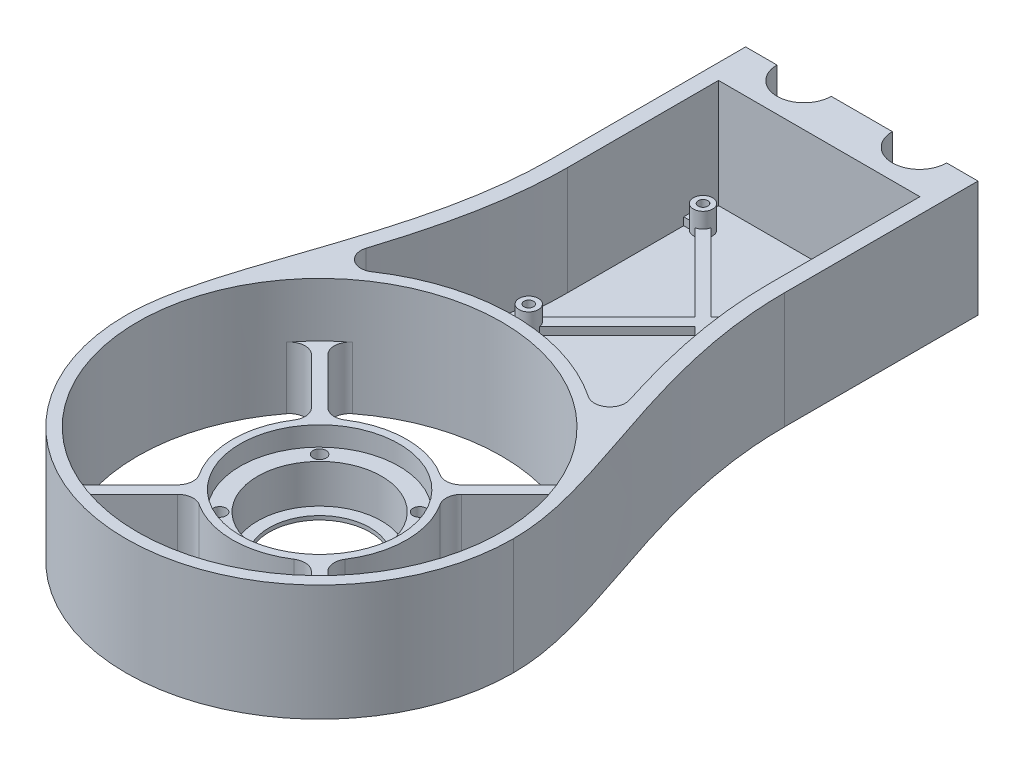
SolidWorks part; units mm, degrees
material "3.1355 (EN-AW 2024)"
ref_plane "Front" through (0, 0, 0) normal (0, 0, 1) x (1, 0, 0)
ref_plane "Top" through (0, 0, 0) normal (0, 1, 0) x (1, 0, 0)
ref_plane "Right" through (0, 0, 0) normal (1, 0, 0) x (0, 0, -1)
sketch "Эскиз1" plane through (0, 0, 0) normal (0, 1, 0) x (1, 0, 0)
  line L0 (0, 0) -> (8.1, 0)
  line L1 (0, 0) -> (0, -100) construction
  line L2 (0, -12.5175) -> (60, -12.5175) construction
  line L3 (8.1, 0) -> (22.1, 0) construction
  line L4 (30, -12.5175) -> (30, 0) construction
  line L5 (60, 0) -> (51.9, 0)
  line L6 (60, 0) -> (60, -100) construction
  line L7 (22.1, 0) -> (37.9, 0)
  line L8 (30, 0) -> (30, -140) construction
  line L9 (0, -80.7644) -> (0, -19.2352) construction
  line L10 (0, 0) -> (0, -50)
  line L11 (60, 0) -> (60, -50)
  arc A0 (22.1, 0) -> (8.1, 0) centre (15.1, 0) cw
  arc A1 (37.9, 0) -> (51.9, 0) centre (44.9, 0) ccw
  circle A2 centre (30, -140) radius 47 construction
  circle A3 centre (30, -140) radius 50 construction
  arc A4 (-20, -140) -> (80, -140) centre (30, -140) ccw
  spline S0 degree 3 poles (0, -50) (0, -86.1164) (-20.1607, -116.6426) (-20, -140) knots 0 0 0 0 1 1 1 1
  spline S1 degree 3 poles (60, -50) (60, -86.1164) (80.1607, -116.6426) (80, -140) knots 0 0 0 0 1 1 1 1
  dimension "D3" = 7
  dimension "D5" = 94
  dimension "D6" = 100
  dimension "D1" = 60
  dimension "D2" = 29.8
  dimension "D4" = 140
extrude "Бобышка-Вытянуть1" add sketch "Эскиз1" along normal blind 30
sketch "Эскиз2" plane through (0, 0, 0) normal (0, -1, 0) x (1, 0, 0)
  line L10 (3, 50) -> (3, 3)
  line L11 (3, 3) -> (5.5606, 3)
  line L12 (24.6394, 3) -> (35.3606, 3)
  line L13 (54.4394, 3) -> (57, 3)
  line L14 (57, 3) -> (57, 50)
  line L15 (0, 50) -> (0, 0)
  line L16 (60, 0) -> (60, 50)
  line L17 (51.9, 0) -> (60, 0)
  line L18 (22.1, 0) -> (37.9, 0)
  line L19 (0, 0) -> (8.1, 0)
  line L20 (0, 50) -> (0, 0) construction
  line L21 (60, 0) -> (60, 50) construction
  line L22 (51.9, 0) -> (60, 0) construction
  line L23 (22.1, 0) -> (37.9, 0) construction
  line L24 (0, 0) -> (8.1, 0) construction
  arc A6 (24.6394, 3) -> (5.5606, 3) centre (15.1, 0) ccw
  arc A7 (54.4394, 3) -> (35.3606, 3) centre (44.9, 0) ccw
  arc A8 (77, 139.9896) -> (-17, 139.9896) centre (30, 140) ccw
  arc A9 (80, 140) -> (-20, 140) centre (30, 140) ccw
  arc A10 (51.9, 0) -> (37.9, 0) centre (44.9, 0) ccw
  arc A11 (22.1, 0) -> (8.1, 0) centre (15.1, 0) ccw
  arc A12 (80, 140) -> (-20, 140) centre (30, 140) ccw construction
  arc A13 (51.9, 0) -> (37.9, 0) centre (44.9, 0) ccw construction
  arc A14 (22.1, 0) -> (8.1, 0) centre (15.1, 0) ccw construction
  spline S4 degree 1 poles (57, 50) (77, 139.9896) knots 0 0 1 1 construction
  spline S5 degree 1 poles (-17, 139.9896) (3, 50) knots 0 0 1 1 construction
  spline S6 degree 3 poles (1977.4891, 89.0603) (-2125.3468, 381.0882) (2082.0698, -1.9555) (-1932.4354, -415.3328) knots -3.22742 -3.22742 -3.22742 -3.22742 4.19175 4.19175 4.19175 4.19175 only from (-20, 140) to (0, 50)
  spline S7 degree 3 poles (1992.5098, -415.3405) (-2022.1214, -1.9603) (2185.3713, 381.0899) (-1917.4879, 89.0604) knots -3.191796 -3.191796 -3.191796 -3.191796 4.227419 4.227419 4.227419 4.227419 only from (60, 50) to (80, 140)
  spline S8 degree 3 poles (-20, 140) (-20.1607, 116.6426) (0, 86.1164) (0, 50) knots 0 0 0 0 1 1 1 1 construction
  spline S9 degree 3 poles (60, 50) (60, 86.1164) (80.1607, 116.6426) (80, 140) knots 0 0 0 0 1 1 1 1 construction
  spline S10 degree 3 poles (57, 50) (57, 51.1576) (57.0406, 53.4814) (57.2737, 58.0563) (57.8301, 63.6858) (58.8583, 70.2789) (60.6259, 78.8547) (63.4225, 89.1628) (67.2235, 100.8568) (70.9828, 111.8512) (73.6804, 120.3995) (75.3444, 126.839) (76.2902, 131.4603) (76.7834, 135.1232) (76.9778, 137.9484) (77.0049, 139.3044) (77, 139.9896) knots 0 0 0 0 0.031255 0.06251 0.12502 0.18753 0.25004 0.375059 0.500079 0.625099 0.750119 0.812629 0.875139 0.937649 0.968904 1.000159 1.000159 1.000159 1.000159
  spline S11 degree 3 poles (-17, 139.9896) (-17.0049, 139.3044) (-16.9778, 137.9484) (-16.7834, 135.1232) (-16.2902, 131.4603) (-15.3444, 126.839) (-13.6804, 120.3995) (-10.9828, 111.8512) (-7.2235, 100.8568) (-3.4225, 89.1628) (-0.6259, 78.8547) (1.1417, 70.2789) (2.1699, 63.6858) (2.7263, 58.0563) (2.9594, 53.4814) (3, 51.1576) (3, 50) knots -0.000159 -0.000159 -0.000159 -0.000159 0.031096 0.062351 0.124861 0.187371 0.249881 0.374901 0.499921 0.624941 0.74996 0.81247 0.87498 0.93749 0.968745 1 1 1 1
  dimension "D1" = 0
  dimension "D2" = 3
extrude "Вырез-Вытянуть1" cut sketch "Эскиз2" against normal through all
sketch "Эскиз3" plane through (0, 0, 0) normal (0, -1, 0) x (1, 0, 0)
  circle A0 centre (30, 140) radius 13
  circle A1 centre (30, 140) radius 22.5
  dimension "D1" = 26
  dimension "D2" = 45
extrude "Бобышка-Вытянуть2" add sketch "Эскиз3" against normal blind 16 separate body
sketch "Эскиз4" plane through (0, 16, 0) normal (0, 1, 0) x (1, 0, 0)
  circle A2 centre (30, -140) radius 20.5
  dimension "D1" = 41
extrude "Вырез-Вытянуть2" cut sketch "Эскиз4" against normal blind 5
sketch "Эскиз5" plane through (0, 11, 0) normal (0, 1, 0) x (1, 0, 0)
  circle A0 centre (30, -140) radius 16
  dimension "D1" = 32
extrude "Вырез-Вытянуть3" cut sketch "Эскиз5" against normal blind 10
sketch "Эскиз6" plane through (0, 11, 0) normal (0, 1, 0) x (1, 0, 0)
  line L0 (30, -140) -> (11.75, -140) construction
  line L1 (30, -140) -> (17.0953, -127.0953) construction
  line L2 (30, -140) -> (42.9047, -127.0953) construction
  line L3 (30, -140) -> (42.9047, -152.9047) construction
  line L4 (30, -140) -> (17.0953, -152.9047) construction
  circle A0 centre (30, -140) radius 18.25 construction
  point P11 (30, -140)
  dimension "D1" = 36.5
  dimension "D2" = 45
  dimension "D3" = 4
hole_wizard "Отверстие с зазором M31" positions "Эскиз8" profile "Эскиз7" hole size "M3" standard "Ansi Metric" end condition through all
sketch "Эскиз8" plane through (0, 11, 0) normal (0, 1, 0) x (1, 0, 0)
  point P0 (17.0953, -127.0953)
  point P3 (42.9047, -127.0953)
  point P6 (42.9047, -152.9047)
  point P9 (17.0953, -152.9047)
sketch "Эскиз7" plane through (17.0953, 11, 127.0953) normal (1, 0, 0) x (0, 0, 1)
  line L0 (0, 0) -> (0, 11)
  line L1 (0, 11) -> (1.7, 11)
  line L2 (1.7, 11) -> (1.7, 0)
  line L5 (1.7, 0) -> (0, 0)
  line L11 (0, -6.35) -> (0, 107.95) construction
  dimension "Диаметр сквозного отверстия" = 3.4
  dimension "Глубина сквозного отверстия" = 11
sketch "Эскиз9" plane through (0, 0, 0) normal (0, -1, 0) x (1, 0, 0)
  arc A0 (-10.5903, 110.8036) -> (70.5903, 110.8036) centre (30, 140) ccw
  arc A2 (-17, 139.9896) -> (77, 139.9896) centre (30, 140) ccw
  spline S1 degree 3 poles (176.8305, 2130.3757) (16.1333, 171.6325) (-19.1296, 169.2303) (-16.7834, 135.1232) (-16.2902, 131.4603) (-15.3444, 126.839) (-13.6804, 120.3995) (-10.9828, 111.8512) (-7.2235, 100.8568) (-3.4225, 89.1628) (-0.6259, 78.8547) (1.1417, 70.2789) (2.1699, 63.6858) (2.7263, 58.0563) (6.1081, -8.3152) (-50.2326, -100.9507) (-382.6813, 2011.3686) knots -1.384464 -1.384464 -1.384464 -1.384464 0.031096 0.062351 0.124861 0.187371 0.249881 0.374901 0.499921 0.624941 0.74996 0.81247 0.87498 0.93749 0.968745 2.688741 2.688741 2.688741 2.688741 only from (-17, 139.9896) to (3, 50) construction
  spline S2 degree 3 poles (442.6854, 2011.3946) (110.2331, -100.9514) (53.8919, -8.3154) (57.2737, 58.0563) (57.8301, 63.6858) (58.8583, 70.2789) (60.6259, 78.8547) (63.4225, 89.1628) (67.2235, 100.8568) (70.9828, 111.8512) (73.6804, 120.3995) (75.3444, 126.839) (76.2902, 131.4603) (76.7834, 135.1232) (79.1296, 169.2304) (43.8663, 171.6325) (-116.8331, 2130.4078) knots -1.688748 -1.688748 -1.688748 -1.688748 0.031255 0.06251 0.12502 0.18753 0.25004 0.375059 0.500079 0.625099 0.750119 0.812629 0.875139 0.937649 0.968904 2.384472 2.384472 2.384472 2.384472 only from (57, 50) to (77, 139.9896) construction
  spline S3 degree 3 poles (70.5903, 110.8036) (70.6927, 111.1128) (71.9682, 114.9738) (73.6804, 120.3995) (75.3444, 126.839) (76.2902, 131.4603) (76.7834, 135.1232) (76.9778, 137.9484) (77.0049, 139.3044) (77, 139.9896) knots 0.614251 0.614251 0.614251 0.614251 0.625099 0.750119 0.812629 0.875139 0.937649 0.968904 1.000159 1.000159 1.000159 1.000159
  spline S4 degree 3 poles (-17, 139.9896) (-17.0049, 139.3044) (-16.9778, 137.9484) (-16.7834, 135.1232) (-16.2902, 131.4603) (-15.3444, 126.839) (-13.6804, 120.3995) (-11.9682, 114.9738) (-10.6927, 111.1128) (-10.5903, 110.8036) knots -0.000159 -0.000159 -0.000159 -0.000159 0.031096 0.062351 0.124861 0.187371 0.249881 0.374901 0.385749 0.385749 0.385749 0.385749
extrude "Бобышка-Вытянуть3" add sketch "Эскиз9" against normal up to surface (16 mm away) up to face at (30, 16, 160.5)
sketch "Эскиз10" plane through (0, 0, 0) normal (0, -1, 0) x (1, 0, 0)
  line L0 (30, 140) -> (-3.2267, 106.7587) construction
  line L1 (30, 140) -> (-17, 139.9896) construction
  line L2 (13.0616, 154.8101) -> (-4.2848, 172.1489)
  line L3 (15.1899, 123.0616) -> (-2.1489, 105.7152)
  line L4 (13.068, 125.1825) -> (-4.2708, 107.8362)
  line L5 (31.0609, 138.9396) -> (-2.1658, 105.6982) construction
  line L6 (15.1825, 156.932) -> (-2.1638, 174.2708)
  line L7 (44.8101, 156.9384) -> (62.1489, 174.2848)
  line L8 (46.932, 154.8175) -> (64.2708, 172.1638)
  line L9 (46.9384, 125.1899) -> (64.2848, 107.8511)
  line L10 (44.8175, 123.068) -> (62.1638, 105.7292)
  circle A0 centre (30, 140) radius 22.5 construction
  arc A1 (13.068, 125.1825) -> (15.1899, 123.0616) centre (30, 140) ccw
  circle A2 centre (30, 140) radius 47 construction
  arc A3 (-4.2708, 107.8362) -> (-2.1489, 105.7152) centre (30, 140) ccw
  arc A4 (-2.1638, 174.2708) -> (-4.2848, 172.1489) centre (30, 140) ccw
  arc A5 (15.1825, 156.932) -> (13.0616, 154.8101) centre (30, 140) ccw
  arc A6 (64.2708, 172.1638) -> (62.1489, 174.2848) centre (30, 140) ccw
  arc A7 (46.932, 154.8175) -> (44.8101, 156.9384) centre (30, 140) ccw
  arc A8 (62.1638, 105.7292) -> (64.2848, 107.8511) centre (30, 140) ccw
  arc A9 (44.8175, 123.068) -> (46.9384, 125.1899) centre (30, 140) ccw
  point P5 (28.9391, 141.0604)
  point P9 (-4.2877, 107.8192)
  point P29 (30, 140)
  point P36 (30, 140)
  dimension "D1" = 45
  dimension "D2" = 4
  dimension "D3" = 1.5
extrude "Бобышка-Вытянуть4" add sketch "Эскиз10" against normal up to surface (16 mm away) up to face at (30, 16, 160.5)
fillet "Скругление1" radius 4 2 edges
fillet "Скругление2" radius 4 16 edges at (13.068, 8, 125.1825) (-4.2708, 8, 107.8362) (13.0616, 8, 154.8101) (-4.2848, 8, 172.1489) (-2.1638, 8, 174.2708) (15.1825, 8, 156.932) (44.8101, 8, 156.9384) (62.1489, 8, 174.2848) (46.932, 8, 154.8175) (64.2708, 8, 172.1638) (46.9384, 8, 125.1899) (64.2848, 8, 107.8511) (44.8175, 8, 123.068) (15.1899, 8, 123.0616) (-2.1489, 8, 105.7152) (62.1638, 8, 105.7292)
sketch "Эскиз11" plane through (0, 30, 0) normal (0, 1, 0) x (1, 0, 0)
  line L0 (3, -50) -> (3, -3) construction
  line L1 (3, -10) -> (57, -10)
  line L2 (57, -3) -> (57, -50) construction
  line L3 (54.4394, -3) -> (57, -3) construction
  line L4 (24.6394, -3) -> (35.3606, -3) construction
  line L5 (3, -3) -> (5.5606, -3) construction
  line L6 (54.4394, -3) -> (57, -3)
  line L7 (24.6394, -3) -> (35.3606, -3)
  line L8 (3, -3) -> (5.5606, -3)
  line L9 (3, -10) -> (3, -3)
  line L10 (57, -3) -> (57, -10)
  arc A0 (5.5606, -3) -> (24.6394, -3) centre (15.1, 0) ccw construction
  arc A1 (5.5606, -3) -> (24.6394, -3) centre (15.1, 0) ccw
  arc A2 (35.3606, -3) -> (54.4394, -3) centre (44.9, 0) ccw construction
  arc A3 (35.3606, -3) -> (54.4394, -3) centre (44.9, 0) ccw
  line M2 (3, -50) -> (3, -3)
  line M3 (3, -3) -> (5.5606, -3)
  arc M4 (5.5606, -3) -> (24.6394, -3) centre (15.1, 0) ccw
  line M5 (24.6394, -3) -> (35.3606, -3)
  arc M6 (35.3606, -3) -> (54.4394, -3) centre (44.9, 0) ccw
  line M7 (54.4394, -3) -> (57, -3)
  line M8 (57, -3) -> (57, -50)
extrude "Бобышка-Вытянуть5" add sketch "Эскиз11" against normal through all contours L1 M4 M6 M5 | L1 M6 M8 M7 | L1 M2 M4 M3
sketch "Эскиз12" plane through (0, 16, 0) normal (0, 1, 0) x (1, 0, 0)
  arc A0 (59.1694, -99.3903) -> (0.8306, -99.3903) centre (30, -140) ccw construction
  arc A1 (-5.3129, -94.9233) -> (0.8306, -99.3903) centre (-1.5029, -96.1415) ccw construction
  arc A2 (59.1694, -99.3903) -> (65.3129, -94.9233) centre (61.5029, -96.1415) ccw construction
  arc A3 (59.1694, -99.3903) -> (0.8306, -99.3903) centre (30, -140) ccw
  arc A4 (-5.3129, -94.9233) -> (0.8306, -99.3903) centre (-1.5029, -96.1415) ccw
  arc A5 (59.1694, -99.3903) -> (65.3129, -94.9233) centre (61.5029, -96.1415) ccw
  arc A7 (58.7182, -102.7943) -> (1.298, -102.7818) centre (30, -140) ccw construction
  arc A8 (77, -139.9896) -> (-17, -139.9896) centre (30, -140) ccw
  spline S0 degree 3 poles (-1914.7367, 431.9839) (72.5207, 220.6611) (28.2156, 2.7872) (-10.9828, -111.8512) (-13.6804, -120.3995) (-15.3444, -126.839) (-16.2902, -131.4603) (-16.7834, -135.1232) (-19.1296, -169.2301) (16.1331, -171.6324) (176.8285, -2130.3521) knots -3.597718 -3.597718 -3.597718 -3.597718 0.06297 0.187989 0.313009 0.375519 0.438029 0.500539 0.531794 1.947349 1.947349 1.947349 1.947349 only from (-5.3129, -94.9233) to (-17, -139.9896) construction
  spline S1 degree 3 poles (-5.3129, -94.9233) (-5.9422, -96.8917) (-7.8438, -102.671) (-10.9828, -111.8512) (-13.6804, -120.3995) (-15.3444, -126.839) (-16.2902, -131.4603) (-16.7834, -135.1232) (-16.9778, -137.9484) (-17.0049, -139.3044) (-17, -139.9896) knots -0.000159 -0.000159 -0.000159 -0.000159 0.06297 0.187989 0.313009 0.375519 0.438029 0.500539 0.531794 0.563049 0.563049 0.563049 0.563049
  spline S2 degree 3 poles (-116.8284, -2130.351) (43.8669, -171.6324) (79.1296, -169.2301) (76.7834, -135.1232) (76.2902, -131.4603) (75.3444, -126.839) (73.6804, -120.3995) (70.9828, -111.8512) (31.7842, 2.7877) (-12.5211, 220.6632) (1974.7671, 431.9871) knots -0.947348 -0.947348 -0.947348 -0.947348 0.468206 0.499461 0.561971 0.624481 0.686991 0.812011 0.93703 4.597736 4.597736 4.597736 4.597736 only from (77, -139.9896) to (65.3129, -94.9233) construction
  spline S3 degree 3 poles (77, -139.9896) (77.0049, -139.3044) (76.9778, -137.9484) (76.7834, -135.1232) (76.2902, -131.4603) (75.3444, -126.839) (73.6804, -120.3995) (70.9828, -111.8512) (67.8438, -102.671) (65.9422, -96.8917) (65.3129, -94.9233) knots 0.436951 0.436951 0.436951 0.436951 0.468206 0.499461 0.561971 0.624481 0.686991 0.812011 0.93703 1.000159 1.000159 1.000159 1.000159
extrude "Бобышка-Вытянуть6" add sketch "Эскиз12" along normal up to surface (14 mm away) up to face at (26.6667, 30, 74.4983)
sketch "Эскиз13" plane through (0, 30, 0) normal (0, 1, 0) x (1, 0, 0)
  line L3 (3, -50) -> (3, -10) construction
  line L4 (3, -10) -> (57, -10) construction
  line L5 (57, -10) -> (57, -50) construction
  line L6 (4, -50) -> (4, -11)
  line L7 (4, -11) -> (56, -11)
  line L8 (56, -11) -> (56, -50)
  line L9 (-4.3604, -95.2279) -> (-5.1661, -97.7479)
  line L10 (64.3604, -95.2279) -> (65.1661, -97.7479)
  line L12 (3, -50) -> (3, -10)
  line L13 (3, -10) -> (57, -10)
  line L14 (57, -10) -> (57, -50)
  arc A0 (-5.3129, -94.9233) -> (0.8306, -99.3903) centre (-1.5029, -96.1415) ccw construction
  arc A1 (-5.3129, -94.9233) -> (-5.1661, -97.7479) centre (-1.5029, -96.1415) ccw
  arc A2 (59.1694, -99.3903) -> (65.3129, -94.9233) centre (61.5029, -96.1415) ccw construction
  arc A4 (65.1661, -97.7479) -> (65.3129, -94.9233) centre (61.5029, -96.1415) ccw
  spline S2 degree 3 poles (1990.0869, -28.6531) (-145.5362, -228.9712) (-36.4686, -210.9677) (-0.6259, -78.8547) (1.1417, -70.2789) (2.1699, -63.6858) (2.7263, -58.0563) (6.1081, 8.3156) (-50.2334, 100.952) (-382.6884, -2011.4141) knots -3.1933 -3.1933 -3.1933 -3.1933 0.624941 0.74996 0.81247 0.87498 0.93749 0.968745 2.688753 2.688753 2.688753 2.688753 only from (-5.3129, -94.9233) to (3, -50) construction
  spline S3 degree 3 poles (442.6888, -2011.4164) (110.2335, 100.952) (53.8919, 8.3156) (57.2737, -58.0563) (57.8301, -63.6858) (58.8583, -70.2789) (60.6259, -78.8547) (96.4685, -210.9671) (205.5353, -228.971) (-1930.0571, -28.6559) knots -1.688754 -1.688754 -1.688754 -1.688754 0.031255 0.06251 0.12502 0.18753 0.25004 0.375059 4.193282 4.193282 4.193282 4.193282 only from (57, -50) to (65.3129, -94.9233) construction
  spline S4 degree 1 poles (-4.3604, -95.2279) (4, -50) knots 0 0 1 1 construction
  spline S5 degree 1 poles (56, -50) (64.3604, -95.2279) knots 0 0 1 1 construction
  spline S6 degree 3 poles (-4.3604, -95.2279) (-3.8086, -93.502) (-2.7375, -90.0676) (-0.6784, -82.9518) (1.5892, -73.7478) (3.1808, -64.0885) (3.8747, -56.1319) (4, -52.035) (4, -50) knots 0.563049 0.563049 0.563049 0.563049 0.617668 0.672287 0.781524 0.890762 0.945381 1 1 1 1
  spline S7 degree 3 poles (56, -50) (56, -52.035) (56.1253, -56.1319) (56.8192, -64.0885) (58.4108, -73.7478) (60.6784, -82.9518) (62.7375, -90.0676) (63.8086, -93.502) (64.3604, -95.2279) knots 0 0 0 0 0.054619 0.109238 0.218476 0.327713 0.382332 0.436951 0.436951 0.436951 0.436951
  spline S8 degree 3 poles (-5.3129, -94.9233) (-4.6959, -92.9935) (-2.8576, -87.0808) (-0.6259, -78.8547) (1.1417, -70.2789) (2.1699, -63.6858) (2.7263, -58.0563) (2.9594, -53.4814) (3, -51.1576) (3, -50) knots 0.563049 0.563049 0.563049 0.563049 0.624941 0.74996 0.81247 0.87498 0.93749 0.968745 1 1 1 1
  spline S9 degree 3 poles (57, -50) (57, -51.1576) (57.0406, -53.4814) (57.2737, -58.0563) (57.8301, -63.6858) (58.8583, -70.2789) (60.6259, -78.8547) (62.8576, -87.0808) (64.6959, -92.9935) (65.3129, -94.9233) knots 0 0 0 0 0.031255 0.06251 0.12502 0.18753 0.25004 0.375059 0.436951 0.436951 0.436951 0.436951
  dimension "D1" = 1
extrude "Бобышка-Вытянуть7" add sketch "Эскиз13" against normal up to surface (30 mm away) up to face at (25.3147, 0, 64.1334)
sketch "Эскиз14" plane through (0, 30, 0) normal (0, 1, 0) x (1, 0, 0)
  line L0 (4, -50) -> (56, -50)
  line L1 (-5.1661, -97.7479) -> (-4.3604, -95.2279) construction
  line L2 (-8.4599, -108.0495) -> (-4.3604, -95.2279)
  line L3 (64.3604, -95.2279) -> (65.1661, -97.7479) construction
  line L4 (64.3604, -95.2279) -> (68.4599, -108.0495)
  arc A0 (59.1694, -99.3903) -> (0.8306, -99.3903) centre (30, -140) ccw construction
  arc A1 (68.4599, -108.0495) -> (-8.4599, -108.0495) centre (30, -140) ccw
  spline S1 degree 3 poles (-385.17, -2058.4209) (-54.6447, -176.3295) (-20.9375, -152.9616) (-0.6784, -82.9518) (1.5892, -73.7478) (3.1808, -64.0885) (10.1833, 16.2006) (-64.7343, 136.1761) (-591.1703, -1957.0915) knots -1.367986 -1.367986 -1.367986 -1.367986 0.617668 0.672287 0.781524 0.890762 0.945381 2.986145 2.986145 2.986145 2.986145 only from (-4.3604, -95.2279) to (4, -50) construction
  spline S3 degree 3 poles (-4.3604, -95.2279) (-3.8086, -93.502) (-2.7375, -90.0676) (-0.6784, -82.9518) (1.5892, -73.7478) (3.1808, -64.0885) (3.8747, -56.1319) (4, -52.035) (4, -50) knots 0.563049 0.563049 0.563049 0.563049 0.617668 0.672287 0.781524 0.890762 0.945381 1 1 1 1
  spline S4 degree 3 poles (651.1712, -1957.0948) (124.7344, 136.1762) (49.8167, 16.2006) (56.8192, -64.0885) (58.4108, -73.7478) (60.6784, -82.9518) (80.9375, -152.9615) (114.6445, -176.3294) (445.1676, -2058.4071) knots -1.986146 -1.986146 -1.986146 -1.986146 0.054619 0.109238 0.218476 0.327713 0.382332 2.367981 2.367981 2.367981 2.367981 only from (56, -50) to (64.3604, -95.2279) construction
  spline S5 degree 3 poles (56, -50) (56, -52.035) (56.1253, -56.1319) (56.8192, -64.0885) (58.4108, -73.7478) (60.6784, -82.9518) (62.7375, -90.0676) (63.8086, -93.502) (64.3604, -95.2279) knots 0 0 0 0 0.054619 0.109238 0.218476 0.327713 0.382332 0.436951 0.436951 0.436951 0.436951
extrude "Вырез-Вытянуть4" cut sketch "Эскиз14" against normal through all
sketch "Эскиз15" plane through (0, 30, 0) normal (0, 1, 0) x (1, 0, 0)
  line L0 (-8.4599, -108.0495) -> (-4.3604, -95.2279) construction
  line L1 (-8.4599, -108.0495) -> (-4.3604, -95.2279)
  line L2 (64.3604, -95.2279) -> (68.4599, -108.0495) construction
  line L3 (64.3604, -95.2279) -> (68.4599, -108.0495)
  arc A1 (68.4599, -108.0495) -> (-8.4599, -108.0495) centre (30, -140) ccw construction
  arc A2 (2.0776, -98.523) -> (-3.9825, -94.039) centre (-0.1562, -95.2048) cw
  arc A3 (63.9825, -94.0392) -> (57.9224, -98.523) centre (60.1562, -95.2048) cw
  arc A4 (68.4599, -108.0495) -> (57.9224, -98.523) centre (30, -140) ccw
  arc A5 (2.0776, -98.523) -> (-8.4599, -108.0495) centre (30, -140) ccw
  spline S0 degree 3 poles (-385.17, -2058.4209) (-54.6447, -176.3295) (-20.9375, -152.9616) (-0.6784, -82.9518) (1.5892, -73.7478) (3.1808, -64.0885) (10.1833, 16.2006) (-64.7343, 136.1761) (-591.1703, -1957.0915) knots -1.367986 -1.367986 -1.367986 -1.367986 0.617668 0.672287 0.781524 0.890762 0.945381 2.986145 2.986145 2.986145 2.986145 only from (-4.3604, -95.2279) to (4, -50) construction
  spline S2 degree 3 poles (-4.3604, -95.2279) (-4.2336, -94.8313) (-4.1077, -94.4352) (-3.9825, -94.039) knots 0.563049 0.563049 0.563049 0.563049 0.575599 0.575599 0.575599 0.575599
  spline S3 degree 3 poles (651.1712, -1957.0948) (124.7344, 136.1762) (49.8167, 16.2006) (56.8192, -64.0885) (58.4108, -73.7478) (60.6784, -82.9518) (80.9375, -152.9615) (114.6445, -176.3294) (445.1676, -2058.4071) knots -1.986146 -1.986146 -1.986146 -1.986146 0.054619 0.109238 0.218476 0.327713 0.382332 2.367981 2.367981 2.367981 2.367981 only from (56, -50) to (64.3604, -95.2279) construction
  spline S4 degree 3 poles (63.9825, -94.0392) (64.1077, -94.4353) (64.2336, -94.8313) (64.3604, -95.2279) knots 0.424402 0.424402 0.424402 0.424402 0.436951 0.436951 0.436951 0.436951
  dimension "D1" = 4
  dimension "D2" = 4
extrude "Бобышка-Вытянуть9" add sketch "Эскиз15" against normal blind 30
sketch "Эскиз16" plane through (0, 0, 0) normal (0, -1, 0) x (1, 0, 0)
  line L6 (-7.8525, 101.9352) -> (-2.0682, 81.4275)
  line L7 (-2.0682, 81.4275) -> (2.4014, 58.8164)
  line L8 (2.4014, 58.8164) -> (2.4014, 39.0974)
  line L9 (2.4014, 39.0974) -> (2.4014, 22.5335)
  line L10 (2.4014, 22.5335) -> (2.4014, 9.3875)
  line L11 (2.4014, 9.3875) -> (57.3515, 9.3875)
  line L12 (57.3515, 9.3875) -> (57.3515, 36.7312)
  line L13 (57.3515, 36.7312) -> (57.3515, 56.976)
  line L14 (57.3515, 56.976) -> (62.6099, 81.4275)
  line L15 (62.6099, 81.4275) -> (67.0202, 101.9352)
  line L16 (67.0202, 101.9352) -> (62.6099, 101.9352)
  line L17 (62.6099, 101.9352) -> (57.3515, 100.8957)
  line L18 (57.3515, 100.8957) -> (53.1046, 97.8523)
  line L19 (53.1046, 97.8523) -> (47.4934, 95.4064)
  line L20 (47.4934, 95.4064) -> (40.9286, 92.5448)
  line L21 (40.9286, 92.5448) -> (34.9313, 92.5448)
  line L22 (34.9313, 92.5448) -> (28.8409, 91.3409)
  line L23 (28.8409, 91.3409) -> (21.7336, 92.8693)
  line L24 (21.7336, 92.8693) -> (13.4158, 94.6581)
  line L25 (13.4158, 94.6581) -> (5.0927, 97.8523)
  line L26 (5.0927, 97.8523) -> (-1.0469, 101.9352)
  line L27 (-1.0469, 101.9352) -> (-7.8525, 101.9352)
extrude "Бобышка-Вытянуть10" add sketch "Эскиз16" against normal blind 2
sketch "Эскиз17" plane through (0, 11, 0) normal (0, 1, 0) x (1, 0, 0)
  circle A0 centre (30, -140) radius 18.25 construction
  point P4 (30, -121.75)
  point P5 (42.9047, -127.0953)
  point P8 (48.25, -140)
  point P9 (42.9047, -152.9047)
  point P10 (30, -158.25)
  point P11 (17.0953, -152.9047)
  point P12 (11.75, -140)
  point P13 (17.0953, -127.0953)
  point P14 (30, -140)
  dimension "D1" = 8
sketch "Эскиз18" plane through (0, 2, 0) normal (0, 1, 0) x (1, 0, 0)
  line L0 (5, -16) -> (55, -16)
  line L1 (7.5, -18.5) -> (52.5, -18.5) construction
  line L2 (7.5, -18.5) -> (7.5, -63.5) construction
  line L3 (7.5, -63.5) -> (52.5, -63.5) construction
  line L4 (52.5, -18.5) -> (52.5, -63.5) construction
  line L5 (55, -16) -> (55, -66)
  line L6 (5, -66) -> (55, -66)
  line L7 (5, -16) -> (5, -66)
  line L10 (4, -50) -> (4, -11) construction
  line L11 (4, -11) -> (56, -11) construction
  circle A0 centre (7.5, -18.5) radius 1.5
  circle A1 centre (52.5, -18.5) radius 1.5
  circle A2 centre (7.5, -63.5) radius 1.5
  circle A3 centre (52.5, -63.5) radius 1.5
  dimension "D4" = 3
  dimension "D1" = 45
  dimension "D3" = 1
  dimension "D5" = 5
  dimension "D2" = 2.5
sketch "Эскиз19" plane through (0, 2, 0) normal (0, 1, 0) x (1, 0, 0)
  circle A0 centre (7.5, -18.5) radius 2.5
  circle A1 centre (52.5, -18.5) radius 2.5
  circle A2 centre (52.5, -63.5) radius 2.5
  circle A3 centre (7.5, -63.5) radius 2.5
  dimension "D1" = 5
extrude "Бобышка-Вытянуть11" add sketch "Эскиз19" along normal blind 6
hole_wizard "Отверстие обработанное метчиком M3x0.51" positions "Эскиз21" profile "Эскиз20" tap size "M3x0.5" standard "Ansi Metric"
sketch "Эскиз21" plane through (0, 8, 0) normal (0, 1, 0) x (1, 0, 0)
  point P0 (7.5, -18.5)
  point P3 (52.5, -18.5)
  point P6 (52.5, -63.5)
  point P9 (7.5, -63.5)
sketch "Эскиз20" plane through (7.5, 8, 18.5) normal (1, 0, 0) x (0, 0, 1)
  line L0 (0, 0) -> (0, 6.7511)
  line L1 (0, 6.7511) -> (1.25, 6)
  line L2 (1.25, 6) -> (1.25, 0)
  line L5 (1.25, 0) -> (0, 0)
  line L10 (0, 6.7511) -> (-1.25, 6) construction
  line L11 (0, -6.35) -> (0, 107.95) construction
  dimension "Диаметр сверла" = 2.5
  dimension "Глубина сверла" = 6
  dimension "Угол заточки сверла" = 118
cosmetic thread "Отверстие резьбы1" parameters "D1"=6, "D2"=3
cosmetic thread "Отверстие резьбы2" parameters "D1"=6, "D2"=3
cosmetic thread "Отверстие резьбы3" parameters "D1"=6, "D2"=3
cosmetic thread "Отверстие резьбы4" parameters "D1"=6, "D2"=3
sketch "Эскиз22" plane through (0, 2, 0) normal (0, 1, 0) x (1, 0, 0)
  line L0 (9.2678, -61.7322) -> (50.7322, -20.2678) construction
  line L1 (9.2678, -20.2678) -> (50.7322, -61.7322) construction
  line L2 (7.8536, -20.9749) -> (27.8787, -41)
  line L3 (9.9749, -63.1464) -> (30, -43.1213)
  line L4 (9.9749, -18.8536) -> (30, -38.8787)
  line L5 (7.8536, -61.0251) -> (27.8787, -41)
  line L6 (32.1213, -41) -> (52.1464, -61.0251)
  line L7 (30, -38.8787) -> (50.0251, -18.8536)
  line L8 (10.3284, -19.2071) -> (51.7929, -60.6716) construction
  line L9 (30, -43.1213) -> (50.0251, -63.1464)
  line L10 (8.2071, -60.6716) -> (49.6716, -19.2071) construction
  line L11 (32.1213, -41) -> (52.1464, -20.9749)
  line L12 (8.2071, -21.3284) -> (49.6716, -62.7929) construction
  line L13 (5, -63.5) -> (3.1375, -63.5) construction
  line L14 (10.3284, -62.7929) -> (51.7929, -21.3284) construction
  line L15 (5, -18.5) -> (4, -18.5) construction
  line L16 (4, -50) -> (4, -11) construction
  line L17 (55, -18.5) -> (56, -18.5) construction
  line L18 (56, -11) -> (56, -50) construction
  line L19 (55, -63.5) -> (56.8625, -63.5) construction
  line L20 (5.5, -17) -> (4, -17)
  line L21 (54.5, -20) -> (56, -20)
  line L22 (54.5, -65) -> (57.0591, -65)
  line L23 (5.5, -62) -> (3.315, -62)
  line L24 (5.5, -20) -> (4, -20)
  line L25 (54.5, -17) -> (56, -17)
  line L26 (54.5, -62) -> (56.685, -62)
  line L27 (5.5, -65) -> (2.9409, -65)
  line L28 (5, -65) -> (3.1375, -65) construction
  line L29 (5, -62) -> (3.1375, -62) construction
  line L30 (4, -20) -> (4, -17)
  line L31 (5, -17) -> (4, -17) construction
  line L32 (5, -20) -> (4, -20) construction
  line L33 (56, -11) -> (56, -50) construction
  line L34 (56, -17) -> (56, -20)
  line L35 (55, -17) -> (56, -17) construction
  line L36 (55, -20) -> (56, -20) construction
  line L37 (55, -65) -> (56.8625, -65) construction
  line L38 (55, -62) -> (56.8625, -62) construction
  line L39 (7.5, -63.5) -> (52.5, -63.5) construction
  line L40 (7.5, -63.5) -> (52.5, -63.5)
  arc A1 (7.8536, -20.9749) -> (9.9749, -18.8536) centre (7.5, -18.5) ccw
  arc A3 (54.5, -20) -> (54.5, -17) centre (52.5, -18.5) ccw
  arc A5 (54.5, -65) -> (54.5, -62) centre (52.5, -63.5) ccw
  arc A7 (10, -63.5) -> (7.8536, -61.0251) centre (7.5, -63.5) ccw
  circle A8 centre (7.5, -18.5) radius 2.5
  circle A9 centre (52.5, -18.5) radius 2.5
  circle A10 centre (52.5, -63.5) radius 2.5
  arc A11 (5.5, -17) -> (5.5, -20) centre (7.5, -18.5) ccw
  arc A12 (50.0251, -18.8536) -> (52.1464, -20.9749) centre (52.5, -18.5) ccw
  arc A13 (52.1464, -61.0251) -> (50, -63.5) centre (52.5, -63.5) ccw
  circle A14 centre (7.5, -63.5) radius 2.5
  arc A15 (5.5, -62) -> (5.5, -65) centre (7.5, -63.5) ccw
  spline S0 degree 3 poles (-3.9825, -94.039) (-3.563, -92.7112) (-2.6192, -89.6589) (-0.6784, -82.9518) (1.5892, -73.7478) (3.1808, -64.0885) (3.8747, -56.1319) (4, -52.035) (4, -50) knots 0.575599 0.575599 0.575599 0.575599 0.617668 0.672287 0.781524 0.890762 0.945381 1 1 1 1 construction
  spline S1 degree 3 poles (651.1606, -1957.0528) (124.7334, 136.1746) (49.8167, 16.2002) (56.8192, -64.0885) (58.4108, -73.7478) (60.6784, -82.9518) (80.9333, -152.9469) (114.6297, -176.3191) (444.9434, -2057.1308) knots -1.986132 -1.986132 -1.986132 -1.986132 0.054619 0.109238 0.218476 0.327713 0.382332 2.367532 2.367532 2.367532 2.367532 only from (56, -50) to (63.9825, -94.0392) construction
  spline S2 degree 3 poles (-384.9424, -2057.1249) (-54.6296, -176.319) (-20.9332, -152.9468) (-0.6784, -82.9518) (1.5892, -73.7478) (3.1808, -64.0885) (10.1832, 16.1998) (-64.7327, 136.1735) (-591.1528, -1957.0216) knots -1.36753 -1.36753 -1.36753 -1.36753 0.617668 0.672287 0.781524 0.890762 0.945381 2.986122 2.986122 2.986122 2.986122 only from (-3.9825, -94.039) to (4, -50) construction
  spline S3 degree 3 poles (2.9409, -65) (3.0739, -64.0316) (3.1992, -63.0317) (3.312, -62.0268) (3.315, -62) knots 0.863647 0.863647 0.863647 0.863647 0.890762 0.891504 0.891504 0.891504 0.891504
  spline S4 degree 3 poles (56.685, -62) (56.688, -62.0268) (56.8008, -63.0317) (56.9261, -64.0316) (57.0591, -65) knots 0.108496 0.108496 0.108496 0.108496 0.109238 0.136353 0.136353 0.136353 0.136353
  circle M1 centre (52.5, -63.5) radius 2.5
  circle M2 centre (7.5, -18.5) radius 2.5
  spline M3 degree 3 poles (4, -50) (4, -52.035) (3.8747, -56.1319) (3.1808, -64.0885) (1.5892, -73.7478) (-0.6784, -82.9518) (-2.7375, -90.0676) (-3.8086, -93.502) (-4.3604, -95.2279) knots 0.563049 0.563049 0.563049 0.563049 0.617668 0.672287 0.781524 0.890762 0.945381 1 1 1 1 only from (4, -50) to (-3.9825, -94.039)
  spline M7 degree 3 poles (64.3604, -95.2279) (63.8086, -93.502) (62.7375, -90.0676) (60.6784, -82.9518) (58.4108, -73.7478) (56.8192, -64.0885) (56.1253, -56.1319) (56, -52.035) (56, -50) knots 0 0 0 0 0.054619 0.109238 0.218476 0.327713 0.382332 0.436951 0.436951 0.436951 0.436951 only from (63.9825, -94.0392) to (56, -50)
  line M8 (56, -50) -> (56, -11)
  line M10 (4, -11) -> (4, -50)
  circle M11 centre (52.5, -18.5) radius 2.5
  circle M12 centre (7.5, -63.5) radius 2.5
  dimension "D1" = 1.5
  dimension "D2" = 1.5
  dimension "D3" = 1.5
  dimension "D4" = 1.5
  dimension "D5" = 0
  dimension "D6" = 0
  dimension "D7" = 0
  dimension "D8" = 0
extrude "Бобышка-Вытянуть12" add sketch "Эскиз22" along normal blind 2 contours L6 L11 L7 L4 L2 L5 L3 L9 M11 M2 M12 M1 | L27 L23 M12 M3 | L24 L20 M2 M10 | L25 L21 M11 M8 | L26 L22 M1 M7
